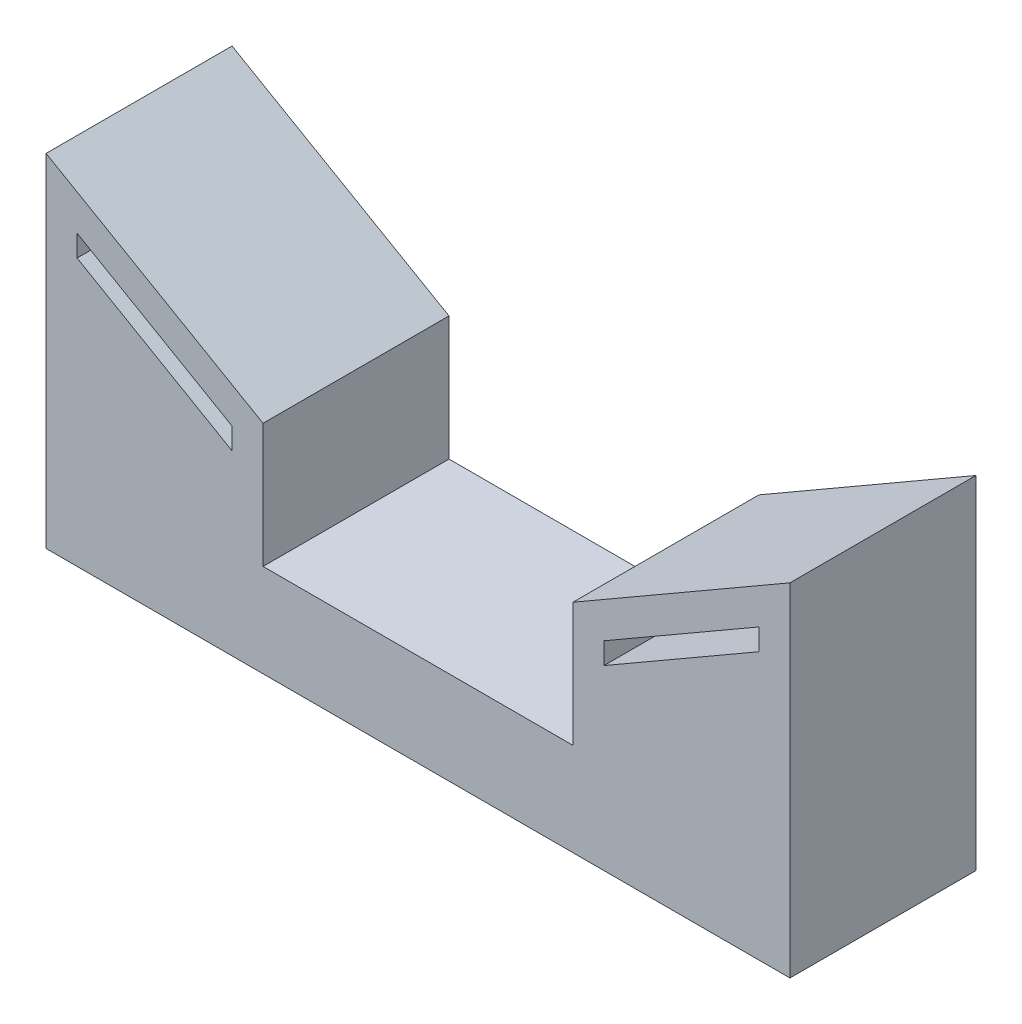
SolidWorks part; units mm, degrees
ref_plane "Plan de face" through (0, 0, 0) normal (0, 0, 1) x (1, 0, 0)
ref_plane "Plan de dessus" through (0, 0, 0) normal (0, 1, 0) x (1, 0, 0)
ref_plane "Plan de droite" through (0, 0, 0) normal (1, 0, 0) x (0, 0, -1)
sketch "Esquisse1" plane through (0, 0, 0) normal (0, 0, 1) x (1, 0, 0)
  line L0 (0, -110.1196) -> (0, 110.1196) construction
  line L1 (-116.3762, 0) -> (116.3762, 0) construction
  line L2 (25, 20) -> (60, 40.2073)
  line L3 (60, 40.2073) -> (0, 40.2073) construction
  line L4 (25, 20) -> (0, 20) construction
  line L5 (25, 20) -> (25, 0)
  line L6 (30, 17.1132) -> (55, 31.547)
  line L7 (60, 0) -> (60, 40.2073)
  line L8 (-60, 0) -> (-60, 40.2073)
  line L10 (-25, 20) -> (-25, 0)
  line L11 (-25, 20) -> (-60, 40.2073)
  line L12 (60, 0) -> (60, -15)
  line L13 (60, -15) -> (-60, -15)
  line L14 (-60, 0) -> (-60, -15)
  line L15 (25, 0) -> (-25, 0)
  line L16 (30, 13.6491) -> (55, 28.0829)
  line L17 (42.5, 30.1036) -> (42.5, 0) construction
  line L18 (30, 17.1132) -> (30, 13.6491)
  line L19 (55, 31.547) -> (55, 28.0829)
  line L20 (55, 30.1036) -> (55, -20.314) construction
  line L22 (29, 13.0718) -> (64, 33.2791) construction
  line L23 (27.5, 15.6699) -> (62.5, 35.8771) construction
  line L24 (-30, 17.1132) -> (-30, 13.6491)
  line L25 (42.5, 30.1036) -> (42.5, -20.314) construction
  line L26 (30, 30.1036) -> (30, -20.314) construction
  line L27 (-30, 13.6491) -> (-55, 28.0829)
  line L28 (-55, 31.547) -> (-55, 28.0829)
  line L29 (-30, 17.1132) -> (-55, 31.547)
  point P3 (0, 0)
  point P7 (0, 0)
  point P39 (0, 0)
  point P40 (0, 0)
  dimension "D1" = 60
  dimension "D2" = 60
  dimension "D3" = 25
  dimension "D4" = 15
  dimension "D5" = 20
  dimension "D6" = 5
  dimension "D8" = 12.5
  dimension "D7" = 3
  dimension "D9" = 12.5
extrude "Boss.-Extru.1" add sketch "Esquisse1" along normal blind 30
